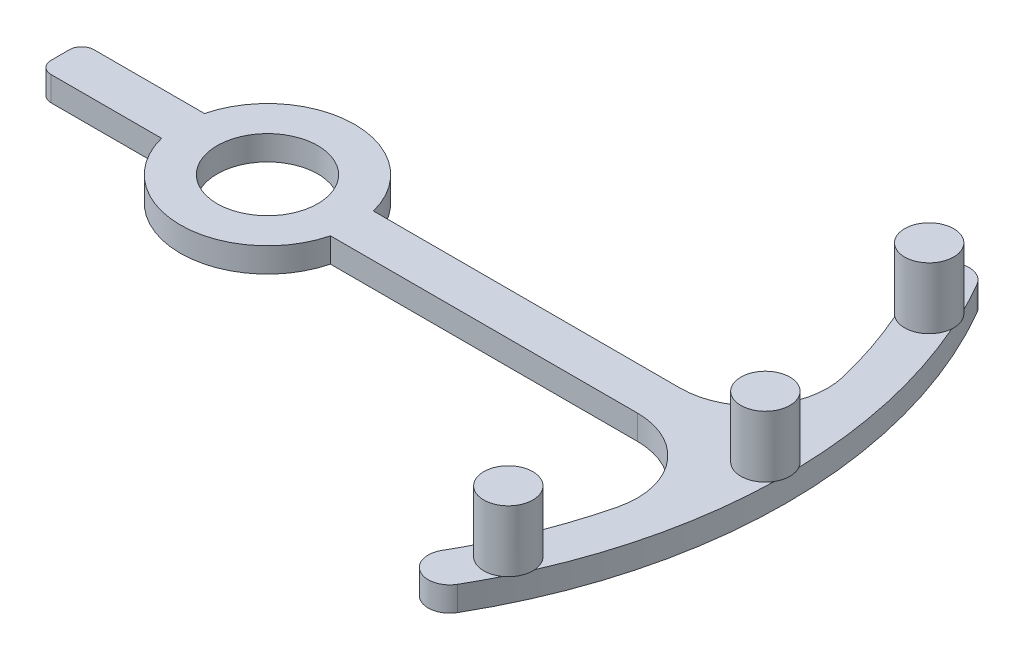
SolidWorks part; units mm, degrees
ref_plane "Front Plane" through (0, 0, 0) normal (0, 0, 1) x (1, 0, 0)
ref_plane "Top Plane" through (0, 0, 0) normal (0, 1, 0) x (1, 0, 0)
ref_plane "Right Plane" through (0, 0, 0) normal (1, 0, 0) x (0, 0, -1)
sketch "Sketch1" plane through (0, 0, 0) normal (0, 1, 0) x (1, 0, 0)
  line L0 (-17.8112, 0) -> (69.2303, 0) construction
  line L1 (6.881, 1.75) -> (31.881, 1.75)
  line L2 (0, 0) -> (33.6099, 19.4047) construction
  line L4 (6.881, -1.75) -> (31.881, -1.75)
  line L5 (-16.8813, 0.7486) -> (-16.8813, -0.7486)
  line L6 (-6.8813, -1.7486) -> (-15.8813, -1.7486)
  line L7 (-6.8813, 1.7486) -> (-15.8813, 1.7486)
  circle A0 centre (0, 0) radius 4.1
  arc A1 (6.881, 1.75) -> (-6.8813, 1.7486) centre (0, 0) ccw
  arc A2 (33.6099, -19.4047) -> (37.7112, -9.1673) centre (0, 0) ccw
  arc A3 (36.641, -21.1547) -> (36.641, 21.1547) centre (0, 0) ccw
  arc A4 (37.7112, 9.1673) -> (33.6099, 19.4047) centre (0, 0) ccw
  arc A5 (33.6099, 19.4047) -> (36.641, 21.1547) centre (35.1255, 20.2797) cw
  arc A6 (33.6099, -19.4047) -> (36.641, -21.1547) centre (35.1255, -20.2797) ccw
  arc A7 (-6.8813, -1.7486) -> (6.881, -1.75) centre (0, 0) ccw
  arc A8 (-15.8813, 1.7486) -> (-16.8813, 0.7486) centre (-15.8813, 0.7486) ccw
  arc A9 (-15.8813, -1.7486) -> (-16.8813, -0.7486) centre (-15.8813, -0.7486) cw
  arc A10 (37.7112, 9.1673) -> (31.881, 1.75) centre (31.881, 7.75) cw
  arc A11 (37.7112, -9.1673) -> (31.881, -1.75) centre (31.881, -7.75) ccw
  point P20 (-16.8813, 1.7486)
  point P26 (-16.8813, -1.7486)
  point P27 (38.7699, 1.75)
  dimension "D1" = 1
  dimension "D3" = 6
  dimension "D4" = 6
  dimension "D2" = 1
  dimension "D5" = 8.2
  dimension "D7" = 7.1
  dimension "D9" = 30
  dimension "D6" = 10
  dimension "D8" = 25
  dimension "D10" = 3.5
  dimension "D11" = 38.8094
extrude "Boss-Extrude1" add sketch "Sketch1" along normal blind 2
sketch "Sketch2" plane through (0, 2, 0) normal (0, 1, 0) x (1, 0, 0)
  line L0 (0, 0) -> (46.512, 21.6889) construction
  line L1 (0, 0) -> (52.2989, 0) construction
  circle A0 centre (36.7593, 17.1412) radius 2
  circle A1 centre (40.5594, 0) radius 2
  circle A2 centre (36.7593, -17.1412) radius 2
  dimension "D2" = 4
  dimension "D3" = 4
  dimension "D1" = 25
extrude "Boss-Extrude2" add sketch "Sketch2" along normal blind 5
